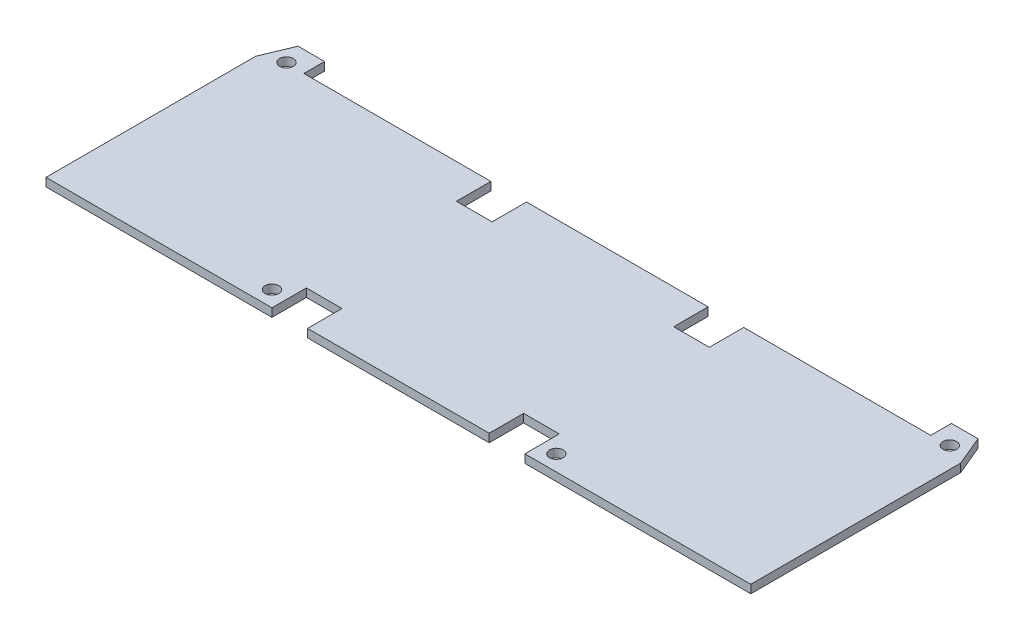
SolidWorks part; units mm, degrees
ref_plane "Plan de face" through (0, 0, 0) normal (0, 0, 1) x (1, 0, 0)
ref_plane "Plan de dessus" through (0, 0, 0) normal (0, 1, 0) x (1, 0, 0)
ref_plane "Plan de droite" through (0, 0, 0) normal (1, 0, 0) x (0, 0, -1)
sketch "Esquisse1" plane through (0, 0, 0) normal (0, 1, 0) x (1, 0, 0)
  line L0 (21.9, 26.4) -> (-21.9, 26.4)
  line L1 (0, 0) -> (0, 26.4) construction
  line L2 (-21.9, 26.4) -> (-21.9, 18.1)
  line L3 (-21.9, 18.1) -> (-30.5, 18.1)
  line L4 (-21.9, 26.4) -> (-30.5, 26.4) construction
  line L5 (-30.5, 18.1) -> (-30.5, 26.4)
  line L6 (-30.5, 26.4) -> (-75.6, 26.4)
  line L7 (-75.6, 26.4) -> (-75.6, 31.4)
  line L8 (-75.6, 31.4) -> (-82, 31.4)
  line L9 (-82, 31.4) -> (-85, 24.2)
  line L10 (-85, 24.2) -> (-85, -26.4)
  line L11 (-85, -26.4) -> (-30.5, -26.4)
  line L12 (-30.5, -26.4) -> (-30.5, -18.1)
  line L13 (-30.5, -18.1) -> (-21.9, -18.1)
  line L14 (-21.9, -18.1) -> (-21.9, -26.4)
  line L15 (-21.9, -26.4) -> (21.9, -26.4)
  line L16 (0, -26.4) -> (0, 0) construction
  line L17 (-21.9, -26.4) -> (-30.5, -26.4) construction
  line L18 (85, -26.4) -> (30.5, -26.4)
  line L19 (30.5, -26.4) -> (30.5, -18.1)
  line L20 (30.5, -18.1) -> (21.9, -18.1)
  line L21 (21.9, -18.1) -> (21.9, -26.4)
  line L22 (21.9, 26.4) -> (21.9, 18.1)
  line L23 (21.9, 18.1) -> (30.5, 18.1)
  line L24 (30.5, 18.1) -> (30.5, 26.4)
  line L25 (30.5, 26.4) -> (75.6, 26.4)
  line L26 (75.6, 26.4) -> (75.6, 31.4)
  line L27 (75.6, 31.4) -> (82, 31.4)
  line L28 (82, 31.4) -> (85, 24.2)
  line L29 (85, 24.2) -> (85, -26.4)
  dimension "D1" = 26.4
  dimension "D2" = 8.6
  dimension "D3" = 21.9
  dimension "D4" = 8.3
  dimension "D5" = 5
  dimension "D6" = 45.1
  dimension "D7" = 6.4
  dimension "D8" = 112.62
  dimension "D9" = 7.8
  dimension "D10" = 50.6
  dimension "D11" = 54.5
  dimension "D12" = 8.3
  dimension "D13" = 8.6
extrude "Boss.-Extru.1" add sketch "Esquisse1" along normal blind 2
sketch "Esquisse2" plane through (0, 2, 0) normal (0, 1, 0) x (1, 0, 0)
  line L0 (0, 0) -> (0, 7.8921) construction
  circle A0 centre (-80, 26.6) radius 1.65
  circle A1 centre (-34.3, -22.6) radius 1.65
  circle A2 centre (34.3, -22.6) radius 1.65
  circle A3 centre (80, 26.6) radius 1.65
  dimension "D1" = 3.3
  dimension "D4" = 3.3
  dimension "D2" = 26.6
  dimension "D3" = 80
  dimension "D5" = 34.3
  dimension "D6" = 22.6
extrude "Enlèv. mat.-Extru.1" cut sketch "Esquisse2" against normal through all both and the other way through all
